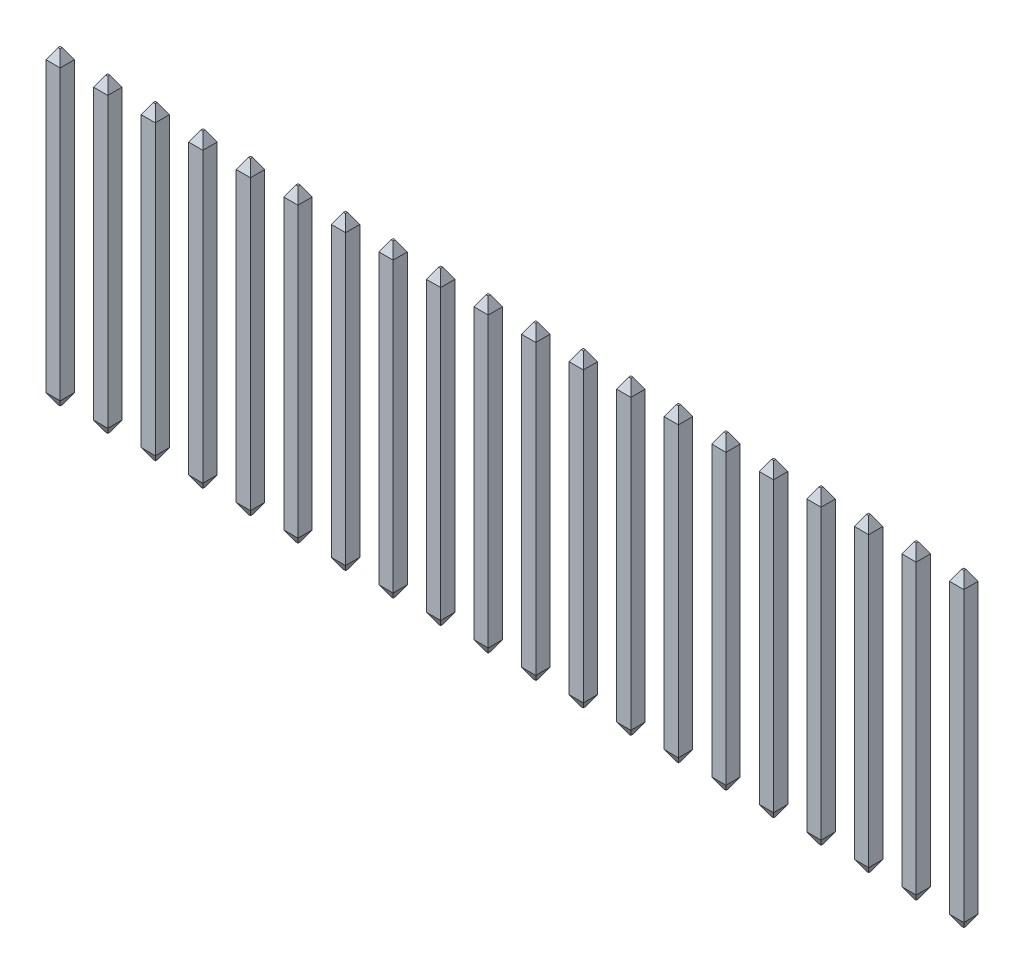
SolidWorks part; units mm, degrees
material "Copper"
ref_plane "Front Plane" through (0, 0, 0) normal (0, 0, 1) x (1, 0, 0)
ref_plane "Top Plane" through (0, 0, 0) normal (0, 1, 0) x (1, 0, 0)
ref_plane "Right Plane" through (0, 0, 0) normal (1, 0, 0) x (0, 0, -1)
sketch "Sketch1" plane through (0, 0, 0) normal (0, 1, 0) x (1, 0, 0)
  line L0 (-12.065, 0) -> (12.065, 0) construction
  line L1 (-10.605, -0.19) -> (-10.605, 0.19)
  line L2 (-12.255, -0.19) -> (-11.875, -0.19)
  line L3 (-12.255, -0.19) -> (-12.255, 0.19)
  line L4 (-12.255, 0.19) -> (-11.875, 0.19)
  line L5 (-11.875, -0.19) -> (-11.875, 0.19)
  line L6 (-12.255, -0.19) -> (-11.875, 0.19) construction
  line L7 (-12.255, 0.19) -> (-11.875, -0.19) construction
  line L8 (-10.985, -0.19) -> (-10.605, 0.19) construction
  line L9 (-10.985, 0.19) -> (-10.605, -0.19) construction
  line L10 (-10.985, 0.19) -> (-10.605, 0.19)
  line L11 (-10.985, -0.19) -> (-10.985, 0.19)
  line L12 (-10.985, -0.19) -> (-10.605, -0.19)
  line L13 (-9.335, -0.19) -> (-9.335, 0.19)
  line L14 (-9.715, -0.19) -> (-9.335, 0.19) construction
  line L15 (-9.715, 0.19) -> (-9.335, -0.19) construction
  line L16 (-9.715, 0.19) -> (-9.335, 0.19)
  line L17 (-9.715, -0.19) -> (-9.715, 0.19)
  line L18 (-9.715, -0.19) -> (-9.335, -0.19)
  line L19 (-8.065, -0.19) -> (-8.065, 0.19)
  line L20 (-8.445, -0.19) -> (-8.065, 0.19) construction
  line L21 (-8.445, 0.19) -> (-8.065, -0.19) construction
  line L22 (-8.445, 0.19) -> (-8.065, 0.19)
  line L23 (-8.445, -0.19) -> (-8.445, 0.19)
  line L24 (-8.445, -0.19) -> (-8.065, -0.19)
  line L25 (-6.795, -0.19) -> (-6.795, 0.19)
  line L26 (-7.175, -0.19) -> (-6.795, 0.19) construction
  line L27 (-7.175, 0.19) -> (-6.795, -0.19) construction
  line L28 (-7.175, 0.19) -> (-6.795, 0.19)
  line L29 (-7.175, -0.19) -> (-7.175, 0.19)
  line L30 (-7.175, -0.19) -> (-6.795, -0.19)
  line L31 (-5.525, -0.19) -> (-5.525, 0.19)
  line L32 (-5.905, -0.19) -> (-5.525, 0.19) construction
  line L33 (-5.905, 0.19) -> (-5.525, -0.19) construction
  line L34 (-5.905, 0.19) -> (-5.525, 0.19)
  line L35 (-5.905, -0.19) -> (-5.905, 0.19)
  line L36 (-5.905, -0.19) -> (-5.525, -0.19)
  line L37 (-4.255, -0.19) -> (-4.255, 0.19)
  line L38 (-4.635, -0.19) -> (-4.255, 0.19) construction
  line L39 (-4.635, 0.19) -> (-4.255, -0.19) construction
  line L40 (-4.635, 0.19) -> (-4.255, 0.19)
  line L41 (-4.635, -0.19) -> (-4.635, 0.19)
  line L42 (-4.635, -0.19) -> (-4.255, -0.19)
  line L43 (-2.985, -0.19) -> (-2.985, 0.19)
  line L44 (-3.365, -0.19) -> (-2.985, 0.19) construction
  line L45 (-3.365, 0.19) -> (-2.985, -0.19) construction
  line L46 (-3.365, 0.19) -> (-2.985, 0.19)
  line L47 (-3.365, -0.19) -> (-3.365, 0.19)
  line L48 (-3.365, -0.19) -> (-2.985, -0.19)
  line L49 (-1.715, -0.19) -> (-1.715, 0.19)
  line L50 (-2.095, -0.19) -> (-1.715, 0.19) construction
  line L51 (-2.095, 0.19) -> (-1.715, -0.19) construction
  line L52 (-2.095, 0.19) -> (-1.715, 0.19)
  line L53 (-2.095, -0.19) -> (-2.095, 0.19)
  line L54 (-2.095, -0.19) -> (-1.715, -0.19)
  line L55 (-0.445, -0.19) -> (-0.445, 0.19)
  line L56 (-0.825, -0.19) -> (-0.445, 0.19) construction
  line L57 (-0.825, 0.19) -> (-0.445, -0.19) construction
  line L58 (-0.825, 0.19) -> (-0.445, 0.19)
  line L59 (-0.825, -0.19) -> (-0.825, 0.19)
  line L60 (-0.825, -0.19) -> (-0.445, -0.19)
  line L61 (0.825, -0.19) -> (0.825, 0.19)
  line L62 (0.445, -0.19) -> (0.825, 0.19) construction
  line L63 (0.445, 0.19) -> (0.825, -0.19) construction
  line L64 (0.445, 0.19) -> (0.825, 0.19)
  line L65 (0.445, -0.19) -> (0.445, 0.19)
  line L66 (0.445, -0.19) -> (0.825, -0.19)
  line L67 (2.095, -0.19) -> (2.095, 0.19)
  line L68 (1.715, -0.19) -> (2.095, 0.19) construction
  line L69 (1.715, 0.19) -> (2.095, -0.19) construction
  line L70 (1.715, 0.19) -> (2.095, 0.19)
  line L71 (1.715, -0.19) -> (1.715, 0.19)
  line L72 (1.715, -0.19) -> (2.095, -0.19)
  line L73 (3.365, -0.19) -> (3.365, 0.19)
  line L74 (2.985, -0.19) -> (3.365, 0.19) construction
  line L75 (2.985, 0.19) -> (3.365, -0.19) construction
  line L76 (2.985, 0.19) -> (3.365, 0.19)
  line L77 (2.985, -0.19) -> (2.985, 0.19)
  line L78 (2.985, -0.19) -> (3.365, -0.19)
  line L79 (4.635, -0.19) -> (4.635, 0.19)
  line L80 (4.255, -0.19) -> (4.635, 0.19) construction
  line L81 (4.255, 0.19) -> (4.635, -0.19) construction
  line L82 (4.255, 0.19) -> (4.635, 0.19)
  line L83 (4.255, -0.19) -> (4.255, 0.19)
  line L84 (4.255, -0.19) -> (4.635, -0.19)
  line L85 (5.905, -0.19) -> (5.905, 0.19)
  line L86 (5.525, -0.19) -> (5.905, 0.19) construction
  line L87 (5.525, 0.19) -> (5.905, -0.19) construction
  line L88 (5.525, 0.19) -> (5.905, 0.19)
  line L89 (5.525, -0.19) -> (5.525, 0.19)
  line L90 (5.525, -0.19) -> (5.905, -0.19)
  line L91 (7.175, -0.19) -> (7.175, 0.19)
  line L92 (6.795, -0.19) -> (7.175, 0.19) construction
  line L93 (6.795, 0.19) -> (7.175, -0.19) construction
  line L94 (6.795, 0.19) -> (7.175, 0.19)
  line L95 (6.795, -0.19) -> (6.795, 0.19)
  line L96 (6.795, -0.19) -> (7.175, -0.19)
  line L97 (8.445, -0.19) -> (8.445, 0.19)
  line L98 (8.065, -0.19) -> (8.445, 0.19) construction
  line L99 (8.065, 0.19) -> (8.445, -0.19) construction
  line L100 (8.065, 0.19) -> (8.445, 0.19)
  line L101 (8.065, -0.19) -> (8.065, 0.19)
  line L102 (8.065, -0.19) -> (8.445, -0.19)
  line L103 (9.715, -0.19) -> (9.715, 0.19)
  line L104 (9.335, -0.19) -> (9.715, 0.19) construction
  line L105 (9.335, 0.19) -> (9.715, -0.19) construction
  line L106 (9.335, 0.19) -> (9.715, 0.19)
  line L107 (9.335, -0.19) -> (9.335, 0.19)
  line L108 (9.335, -0.19) -> (9.715, -0.19)
  line L109 (10.985, -0.19) -> (10.985, 0.19)
  line L110 (10.605, -0.19) -> (10.985, 0.19) construction
  line L111 (10.605, 0.19) -> (10.985, -0.19) construction
  line L112 (10.605, 0.19) -> (10.985, 0.19)
  line L113 (10.605, -0.19) -> (10.605, 0.19)
  line L114 (10.605, -0.19) -> (10.985, -0.19)
  line L115 (12.255, -0.19) -> (12.255, 0.19)
  line L116 (11.875, -0.19) -> (12.255, 0.19) construction
  line L117 (11.875, 0.19) -> (12.255, -0.19) construction
  line L118 (11.875, 0.19) -> (12.255, 0.19)
  line L119 (11.875, -0.19) -> (11.875, 0.19)
  line L120 (11.875, -0.19) -> (12.255, -0.19)
  point P1 (-0.635, 0)
  point P4 (-12.065, 0)
  dimension "D2" = 0.38
  dimension "D1" = 0.635
  dimension "D3" = 20
extrude "Boss-Extrude1" add sketch "Sketch1" along normal blind 5.72 and the other way blind 2.54
sketch "Sketch2" plane through (0, 0, 0) normal (0, 1, 0) x (1, 0, 0)
  line L1 (-12.255, 0.19) -> (12.255, 0.19)
  line L2 (-12.255, 0.19) -> (-12.255, -0.19)
  line L3 (-12.255, -0.19) -> (12.255, -0.19)
  line L4 (12.255, 0.19) -> (12.255, -0.19)
extrude "Boss-Extrude2" add sketch "Sketch2" along normal blind 1
chamfer "Chamfer1" distance 0.28 angle 30 80 edges at (12.255, 5.72, 0) (12.065, 5.72, 0.19) (11.875, 5.72, 0) (12.065, 5.72, -0.19) (10.985, 5.72, 0) (10.795, 5.72, 0.19) (10.605, 5.72, 0) (10.795, 5.72, -0.19) (9.715, 5.72, 0) (9.525, 5.72, 0.19) (9.335, 5.72, 0) (9.525, 5.72, -0.19) (8.445, 5.72, 0) (8.255, 5.72, 0.19) (8.065, 5.72, 0) (8.255, 5.72, -0.19) (7.175, 5.72, 0) (6.985, 5.72, 0.19) (6.795, 5.72, 0) (6.985, 5.72, -0.19) (5.905, 5.72, 0) (5.715, 5.72, 0.19) (5.525, 5.72, 0) (5.715, 5.72, -0.19) (4.635, 5.72, 0) (4.445, 5.72, 0.19) (4.255, 5.72, 0) (4.445, 5.72, -0.19) (3.365, 5.72, 0) (3.175, 5.72, 0.19) (2.985, 5.72, 0) (3.175, 5.72, -0.19) (2.095, 5.72, 0) (1.905, 5.72, 0.19) (1.715, 5.72, 0) (1.905, 5.72, -0.19) (0.825, 5.72, 0) (0.635, 5.72, 0.19) (0.445, 5.72, 0) (0.635, 5.72, -0.19) (-1.715, 5.72, 0) (-1.905, 5.72, 0.19) (-2.095, 5.72, 0) (-1.905, 5.72, -0.19) (-0.445, 5.72, 0) (-0.635, 5.72, 0.19) (-0.825, 5.72, 0) (-0.635, 5.72, -0.19) (-2.985, 5.72, 0) (-3.175, 5.72, 0.19) (-3.365, 5.72, 0) (-3.175, 5.72, -0.19) (-4.255, 5.72, 0) (-4.445, 5.72, 0.19) (-4.635, 5.72, 0) (-4.445, 5.72, -0.19) (-5.525, 5.72, 0) (-5.715, 5.72, 0.19) (-5.905, 5.72, 0) (-5.715, 5.72, -0.19) (-6.795, 5.72, 0) (-6.985, 5.72, 0.19) (-7.175, 5.72, 0) (-6.985, 5.72, -0.19) (-8.065, 5.72, 0) (-8.255, 5.72, 0.19) (-8.445, 5.72, 0) (-8.255, 5.72, -0.19) (-9.335, 5.72, 0) (-9.525, 5.72, 0.19) (-9.715, 5.72, 0) (-9.525, 5.72, -0.19) (-10.605, 5.72, 0) (-10.795, 5.72, 0.19) (-10.985, 5.72, 0) (-10.795, 5.72, -0.19) (-12.065, 5.72, 0.19) (-12.255, 5.72, 0) (-12.065, 5.72, -0.19) (-11.875, 5.72, 0)
chamfer "Chamfer2" distance 0.28 angle 30 80 edges at (11.875, -2.54, 0) (12.065, -2.54, 0.19) (12.255, -2.54, 0) (12.065, -2.54, -0.19) (10.605, -2.54, 0) (10.795, -2.54, 0.19) (10.985, -2.54, 0) (10.795, -2.54, -0.19) (9.335, -2.54, 0) (9.525, -2.54, 0.19) (9.715, -2.54, 0) (9.525, -2.54, -0.19) (8.065, -2.54, 0) (8.255, -2.54, 0.19) (8.445, -2.54, 0) (8.255, -2.54, -0.19) (6.795, -2.54, 0) (6.985, -2.54, 0.19) (7.175, -2.54, 0) (6.985, -2.54, -0.19) (5.525, -2.54, 0) (5.715, -2.54, 0.19) (5.905, -2.54, 0) (5.715, -2.54, -0.19) (4.255, -2.54, 0) (4.445, -2.54, 0.19) (4.635, -2.54, 0) (4.445, -2.54, -0.19) (2.985, -2.54, 0) (3.175, -2.54, 0.19) (3.365, -2.54, 0) (3.175, -2.54, -0.19) (1.715, -2.54, 0) (1.905, -2.54, 0.19) (2.095, -2.54, 0) (1.905, -2.54, -0.19) (0.445, -2.54, 0) (0.635, -2.54, 0.19) (0.825, -2.54, 0) (0.635, -2.54, -0.19) (-0.825, -2.54, 0) (-0.635, -2.54, 0.19) (-0.445, -2.54, 0) (-0.635, -2.54, -0.19) (-2.095, -2.54, 0) (-1.905, -2.54, 0.19) (-1.715, -2.54, 0) (-1.905, -2.54, -0.19) (-3.365, -2.54, 0) (-3.175, -2.54, 0.19) (-2.985, -2.54, 0) (-3.175, -2.54, -0.19) (-4.635, -2.54, 0) (-4.445, -2.54, 0.19) (-4.255, -2.54, 0) (-4.445, -2.54, -0.19) (-5.905, -2.54, 0) (-5.715, -2.54, 0.19) (-5.525, -2.54, 0) (-5.715, -2.54, -0.19) (-7.175, -2.54, 0) (-6.985, -2.54, 0.19) (-6.795, -2.54, 0) (-6.985, -2.54, -0.19) (-8.445, -2.54, 0) (-8.255, -2.54, 0.19) (-8.065, -2.54, 0) (-8.255, -2.54, -0.19) (-9.715, -2.54, 0) (-9.525, -2.54, 0.19) (-9.335, -2.54, 0) (-9.525, -2.54, -0.19) (-10.985, -2.54, 0) (-10.795, -2.54, 0.19) (-10.605, -2.54, 0) (-10.795, -2.54, -0.19) (-12.065, -2.54, -0.19) (-12.255, -2.54, 0) (-12.065, -2.54, 0.19) (-11.875, -2.54, 0)
sketch "Sketch3" plane through (0, 0, 0) normal (0, 1, 0) x (1, 0, 0)
  line L0 (-9.715, 0.19) -> (-9.715, -0.19)
  line L1 (-11.875, 0.19) -> (-10.985, 0.19)
  line L2 (-11.875, 0.19) -> (-11.875, -0.19)
  line L3 (-11.875, -0.19) -> (-10.985, -0.19)
  line L4 (-10.985, 0.19) -> (-10.985, -0.19)
  line L5 (-10.605, 0.19) -> (-9.715, 0.19)
  line L6 (-10.605, 0.19) -> (-10.605, -0.19)
  line L7 (-10.605, -0.19) -> (-9.715, -0.19)
  line L8 (-8.445, 0.19) -> (-8.445, -0.19)
  line L9 (-9.335, 0.19) -> (-8.445, 0.19)
  line L10 (-9.335, 0.19) -> (-9.335, -0.19)
  line L11 (-9.335, -0.19) -> (-8.445, -0.19)
  line L12 (-7.175, 0.19) -> (-7.175, -0.19)
  line L13 (-8.065, 0.19) -> (-7.175, 0.19)
  line L14 (-8.065, 0.19) -> (-8.065, -0.19)
  line L15 (-8.065, -0.19) -> (-7.175, -0.19)
  line L16 (-5.905, 0.19) -> (-5.905, -0.19)
  line L17 (-6.795, 0.19) -> (-5.905, 0.19)
  line L18 (-6.795, 0.19) -> (-6.795, -0.19)
  line L19 (-6.795, -0.19) -> (-5.905, -0.19)
  line L20 (-4.635, 0.19) -> (-4.635, -0.19)
  line L21 (-5.525, 0.19) -> (-4.635, 0.19)
  line L22 (-5.525, 0.19) -> (-5.525, -0.19)
  line L23 (-5.525, -0.19) -> (-4.635, -0.19)
  line L24 (-3.365, 0.19) -> (-3.365, -0.19)
  line L25 (-4.255, 0.19) -> (-3.365, 0.19)
  line L26 (-4.255, 0.19) -> (-4.255, -0.19)
  line L27 (-4.255, -0.19) -> (-3.365, -0.19)
  line L28 (-2.095, 0.19) -> (-2.095, -0.19)
  line L29 (-2.985, 0.19) -> (-2.095, 0.19)
  line L30 (-2.985, 0.19) -> (-2.985, -0.19)
  line L31 (-2.985, -0.19) -> (-2.095, -0.19)
  line L32 (-0.825, 0.19) -> (-0.825, -0.19)
  line L33 (-1.715, 0.19) -> (-0.825, 0.19)
  line L34 (-1.715, 0.19) -> (-1.715, -0.19)
  line L35 (-1.715, -0.19) -> (-0.825, -0.19)
  line L36 (0.445, 0.19) -> (0.445, -0.19)
  line L37 (-0.445, 0.19) -> (0.445, 0.19)
  line L38 (-0.445, 0.19) -> (-0.445, -0.19)
  line L39 (-0.445, -0.19) -> (0.445, -0.19)
  line L40 (1.715, 0.19) -> (1.715, -0.19)
  line L41 (0.825, 0.19) -> (1.715, 0.19)
  line L42 (0.825, 0.19) -> (0.825, -0.19)
  line L43 (0.825, -0.19) -> (1.715, -0.19)
  line L44 (2.985, 0.19) -> (2.985, -0.19)
  line L45 (2.095, 0.19) -> (2.985, 0.19)
  line L46 (2.095, 0.19) -> (2.095, -0.19)
  line L47 (2.095, -0.19) -> (2.985, -0.19)
  line L48 (4.255, 0.19) -> (4.255, -0.19)
  line L49 (3.365, 0.19) -> (4.255, 0.19)
  line L50 (3.365, 0.19) -> (3.365, -0.19)
  line L51 (3.365, -0.19) -> (4.255, -0.19)
  line L52 (5.525, 0.19) -> (5.525, -0.19)
  line L53 (4.635, 0.19) -> (5.525, 0.19)
  line L54 (4.635, 0.19) -> (4.635, -0.19)
  line L55 (4.635, -0.19) -> (5.525, -0.19)
  line L56 (6.795, 0.19) -> (6.795, -0.19)
  line L57 (5.905, 0.19) -> (6.795, 0.19)
  line L58 (5.905, 0.19) -> (5.905, -0.19)
  line L59 (5.905, -0.19) -> (6.795, -0.19)
  line L60 (8.065, 0.19) -> (8.065, -0.19)
  line L61 (7.175, 0.19) -> (8.065, 0.19)
  line L62 (7.175, 0.19) -> (7.175, -0.19)
  line L63 (7.175, -0.19) -> (8.065, -0.19)
  line L64 (9.335, 0.19) -> (9.335, -0.19)
  line L65 (8.445, 0.19) -> (9.335, 0.19)
  line L66 (8.445, 0.19) -> (8.445, -0.19)
  line L67 (8.445, -0.19) -> (9.335, -0.19)
  line L68 (10.605, 0.19) -> (10.605, -0.19)
  line L69 (9.715, 0.19) -> (10.605, 0.19)
  line L70 (9.715, 0.19) -> (9.715, -0.19)
  line L71 (9.715, -0.19) -> (10.605, -0.19)
  line L72 (11.875, 0.19) -> (11.875, -0.19)
  line L73 (10.985, 0.19) -> (11.875, 0.19)
  line L74 (10.985, 0.19) -> (10.985, -0.19)
  line L75 (10.985, -0.19) -> (11.875, -0.19)
  line L76 (13.145, 0.19) -> (13.145, -0.19)
  line L77 (12.255, 0.19) -> (13.145, 0.19)
  line L78 (12.255, 0.19) -> (12.255, -0.19)
  line L79 (12.255, -0.19) -> (13.145, -0.19)
  line L80 (-10.985, 0.19) -> (-9.715, 0.19) construction
  dimension "D2" = 1.27
  dimension "D1" = 20
extrude "Cut-Extrude1" cut sketch "Sketch3" along normal up to surface (1 mm away) up to face at (-11.43, 1, 0)
equation "\"D1@Sketch1\"=1.27/2"
equation "\"D1@Boss-Extrude1\"=2.54+3.18mm"
equation "\"D2@Boss-Extrude1\"=2.54mm"
